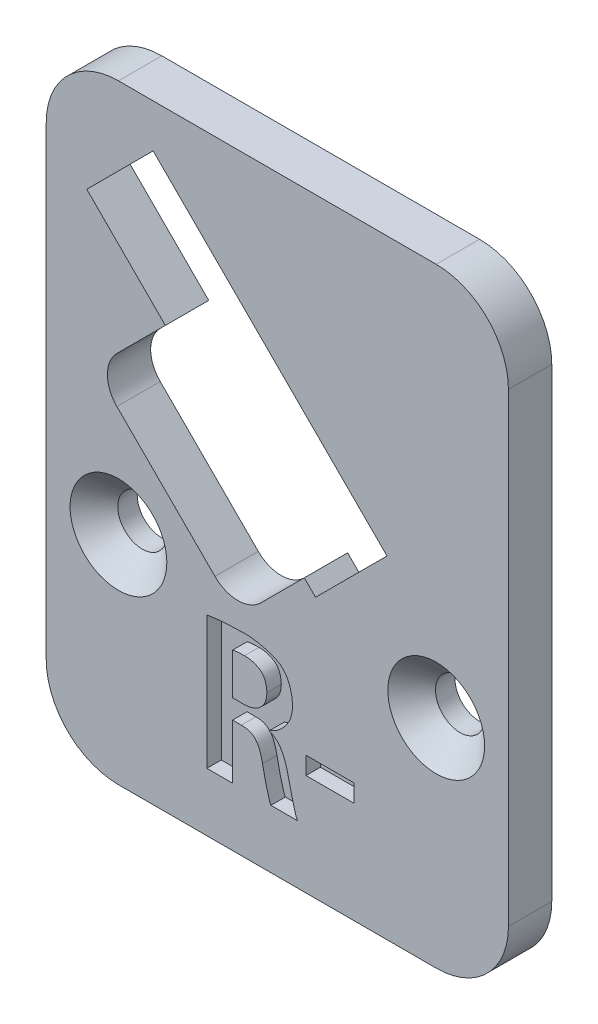
SolidWorks part; units mm, degrees
ref_plane "Front Plane" through (0, 0, 0) normal (0, 0, 1) x (1, 0, 0)
ref_plane "Top Plane" through (0, 0, 0) normal (0, 1, 0) x (1, 0, 0)
ref_plane "Right Plane" through (0, 0, 0) normal (1, 0, 0) x (0, 0, -1)
sketch "Sketch2" plane through (0, 0, 0) normal (0, 0, 1) x (1, 0, 0)
  line L0 (-62.5, 19.7044) -> (-128.5047, 19.7044) construction
  line L34 (-62.5, 22.5) -> (-62.5, -22.5) construction
  line L35 (-30.5, 19.7044) -> (-62.5, 19.7044)
  line L36 (-30.5, 19.7044) -> (-30.5, -22.5)
  line L37 (-30.5, -22.5) -> (-62.5, -22.5)
  line L38 (-62.5, 19.7044) -> (-62.5, -22.5)
  line L39 (-30.5, 19.7044) -> (-62.5, -22.5) construction
  line L40 (-30.5, -22.5) -> (-62.5, 19.7044) construction
  line L41 (-62.5, -22.5) -> (62.5, -22.5) construction
  dimension "D1" = 32
extrude "Boss-Extrude2" add sketch "Sketch2" along normal blind 3
fillet "Fillet1" radius 5 4 edges at (-30.5, -22.5, 1.5) (-62.5, -22.5, 1.5) (-62.5, 19.7044, 1.5) (-30.5, 19.7044, 1.5)
sketch "Sketch3" plane through (0, 0, 3) normal (0, 0, 1) x (1, 0, 0)
  line L0 (-62.5, -18.5) -> (-30.5, -18.5) construction
  line L1 (-62.5, 14.7044) -> (-62.5, -17.5) construction
  line L2 (-30.5, -17.5) -> (-30.5, 14.7044) construction
  line L3 (-57.5, -22.5) -> (-35.5, -22.5) construction
  text T0 "R-" font "@Adobe Gothic Std B" height in points 30
  dimension "D1" = 4
extrude "Cut-Extrude1" cut sketch "Sketch3" against normal blind 1
sketch "Sketch4" plane through (0, 0, 3) normal (0, 0, 1) x (1, 0, 0)
  line L0 (-62.5, -7.5) -> (-30.5, -7.5) construction
  line L1 (-62.5, 14.7044) -> (-62.5, -17.5) construction
  line L2 (-30.5, -17.5) -> (-30.5, 14.7044) construction
  line L3 (-57.5, -22.5) -> (-35.5, -22.5) construction
  point P6 (-57.5, -7.5)
  point P7 (-35.5, -7.5)
  dimension "D1" = 5
  dimension "D2" = 5
  dimension "D3" = 15
hole_wizard "CSK for M3 Countersunk Flat Head Screw1" positions "3DSketch1" profile "Sketch5" countersink size "M3" standard "DIN"
sketch3d "3DSketch1"
  point P0 (-57.5, -7.5, 3)
  point P3 (-35.5, -7.5, 3)
sketch "Sketch5" plane through (-57.5, -7.5, 3) normal (1, 0, 0) x (0, -1, 0)
  line L0 (0, 0) -> (0, 21.0215)
  line L1 (0, 21.0215) -> (1.7, 20)
  line L2 (1.7, 20) -> (1.7, 1.65)
  line L3 (1.7, 1.65) -> (3.35, 0)
  line L5 (3.35, 0) -> (0, 0)
  line L6 (-1.7, 1.65) -> (-3.35, 0) construction
  line L10 (0, 21.0215) -> (-1.7, 20) construction
  line L11 (0, -6.35) -> (0, 107.95) construction
  dimension "Hole Dia." = 3.4
  dimension "Hole Depth" = 20
  dimension "Near C'Sink Dia." = 6.7
  dimension "Near C'Sink Angle" = 90
  dimension "Drill Angle" = 118
sketch "Sketch13" plane through (0, 0, 0) normal (0, 0, -1) x (-1, 0, 0)
  line L0 (55.0991, 16.3509) -> (59.3417, 12.1082) construction
  line L1 (53.897, 6.6635) -> (59.3417, 12.1082) construction
  line L2 (57.4325, 3.128) -> (53.5434, 7.0171) construction
  line L3 (50.6443, -6.4887) -> (57.4325, 0.2996) construction
  line L4 (43.9268, -2.5996) -> (47.8159, -6.4887) construction
  line L5 (43.8561, -4.0845) -> (43.5025, -3.731) construction
  line L6 (44.6339, -3.3067) -> (43.8561, -4.0845) construction
  line L7 (39.2599, 0.5117) -> (43.5025, -3.731) construction
  line L8 (39.2599, 0.5117) -> (40.8862, 2.138) construction
  line L9 (48.0987, 9.3505) -> (40.8862, 2.138) construction
  line L10 (48.0987, 9.3505) -> (55.0991, 16.3509) construction
  line L11 (55.0991, 16.3509) -> (59.3417, 12.1082) construction
  line L12 (53.897, 6.6635) -> (59.3417, 12.1082) construction
  line L13 (57.4325, 3.128) -> (53.897, 6.6635) construction
  line L14 (50.6443, -6.4887) -> (57.4325, 0.2996) construction
  line L15 (44.6339, -3.3067) -> (47.8159, -6.4887) construction
  line L16 (43.8561, -4.0845) -> (43.5025, -3.731) construction
  line L17 (44.6339, -3.3067) -> (43.8561, -4.0845) construction
  line L18 (39.2599, 0.5117) -> (43.5025, -3.731) construction
  line L19 (39.2599, 0.5117) -> (40.8862, 2.138) construction
  line L20 (48.0987, 9.3505) -> (40.8862, 2.138) construction
  line L21 (48.0987, 9.3505) -> (55.0991, 16.3509) construction
  line L22 (55.0991, 16.7044) -> (59.6953, 12.1082)
  line L23 (54.2505, 6.6635) -> (59.6953, 12.1082)
  line L24 (57.6093, 3.3048) -> (54.2505, 6.6635)
  line L25 (50.8211, -6.6654) -> (57.6093, 0.1228)
  line L26 (44.6339, -3.6602) -> (47.6391, -6.6654)
  line L27 (44.6339, -3.6602) -> (43.8561, -4.4381)
  line L28 (43.8561, -4.4381) -> (43.3257, -3.9077)
  line L29 (38.9063, 0.5117) -> (43.3257, -3.9077)
  line L30 (38.9063, 0.5117) -> (40.7095, 2.3148)
  line L31 (47.9219, 9.5273) -> (40.7095, 2.3148)
  line L32 (47.9219, 9.5273) -> (55.0991, 16.7044)
  arc A0 (57.4325, 0.2996) -> (57.4325, 3.128) centre (56.0183, 1.7138) ccw construction
  arc A1 (47.8159, -6.4887) -> (50.6443, -6.4887) centre (49.2301, -5.0745) ccw construction
  arc A2 (57.4325, 0.2996) -> (57.4325, 3.128) centre (56.0183, 1.7138) ccw construction
  arc A3 (47.8159, -6.4887) -> (50.6443, -6.4887) centre (49.2301, -5.0745) ccw construction
  arc A4 (57.6093, 0.1228) -> (57.6093, 3.3048) centre (56.0183, 1.7138) ccw
  arc A5 (47.6391, -6.6654) -> (50.8211, -6.6654) centre (49.2301, -5.0745) ccw
  dimension "D1" = 0.25
extrude "Cut-Extrude3" cut sketch "Sketch13" against normal blind 10
equation "\"D1@Sketch4\"=\"D2@Sketch4\""
